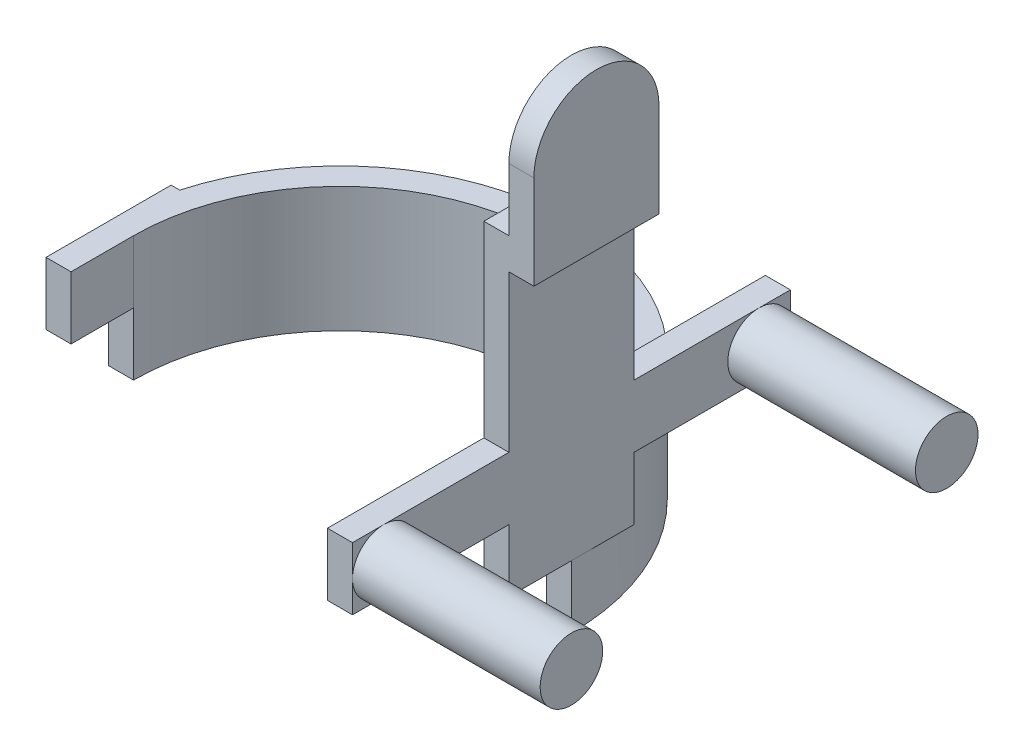
SolidWorks part; units mm, degrees
ref_plane "Front" through (0, 0, 0) normal (0, 0, 1) x (1, 0, 0)
ref_plane "Top" through (0, 0, 0) normal (0, 1, 0) x (1, 0, 0)
ref_plane "Right" through (0, 0, 0) normal (1, 0, 0) x (0, 0, -1)
sketch "草图1" plane through (0, 0, 0) normal (0, 1, 0) x (1, 0, 0)
  line L0 (-72.3418, 0) -> (74, 0) construction
  line L1 (0, 74) -> (0, -74) construction
  line L3 (-74, 20) -> (-71.2461, 20)
  line L4 (-74, 20) -> (-74, -20)
  line L5 (-74, -20) -> (-66, -20)
  line L6 (-66, 0) -> (-66, -20)
  line L7 (74, 20) -> (71.2461, 20)
  line L8 (74, 20) -> (74, -20)
  line L9 (74, -20) -> (66, -20)
  line L10 (66, 0) -> (66, -20)
  arc A0 (71.2461, 20) -> (-71.2461, 20) centre (0, 0) ccw
  arc A1 (66, 0) -> (-66, 0) centre (0, 0) ccw
  dimension "D1" = 40
  dimension "D2" = 20
  dimension "D3" = 8
  dimension "D4" = 8
  dimension "D6" = 40
  dimension "D7" = 20
extrude "凸台-拉伸1" add sketch "草图1" along normal blind 40
sketch "草图2" plane through (0, 40, 0) normal (0, 1, 0) x (1, 0, 0)
  line L1 (-74, -20) -> (-66, -20)
  line L2 (-74, -20) -> (-74, 20)
  line L3 (-74, 20) -> (-66, 20)
  line L4 (-66, -20) -> (-66, 20)
  line L5 (66, -20) -> (74, -20)
  line L6 (66, -20) -> (66, 20)
  line L7 (66, 20) -> (74, 20)
  line L8 (74, -20) -> (74, 20)
  dimension "D1" = 8
extrude "凸台-拉伸2" add sketch "草图2" along normal blind 80
sketch "草图4" plane through (-74, 0, 0) normal (-1, 0, 0) x (0, 0, 1)
  line L1 (-20, 40) -> (29.7839, 40)
  line L2 (-20, 40) -> (-20, 153.9823)
  line L3 (-20, 153.9823) -> (29.7839, 153.9823)
  line L4 (29.7839, 40) -> (29.7839, 153.9823)
extrude "切除-拉伸3" cut sketch "草图4" against normal blind 10
sketch "草图5" plane through (0, 0, 0) normal (0, -1, 0) x (1, 0, 0)
  line L0 (66, 0) -> (66, 20) construction
  line L1 (-71.2461, 20) -> (-66, 20)
  line L3 (-74, 0) -> (-66, 0)
  line L4 (-66, 20) -> (-66, 0)
  line L5 (71.2461, 20) -> (66, 20)
  line L7 (74, 0) -> (66, 0)
  line L8 (66, 20) -> (66, 0)
  arc A0 (-66, 0) -> (66, 0) centre (0, 0) ccw construction
  arc A1 (-74, 0) -> (74, 0) centre (0, 0) ccw
  circle A2 centre (0, 0) radius 84.7622
  arc A3 (71.2461, 20) -> (-71.2461, 20) centre (0, 0) ccw
extrude "切除-拉伸4" cut sketch "草图5" against normal blind 20
sketch "草图6" plane through (74, 0, 0) normal (1, 0, 0) x (0, 0, -1)
  line L0 (66, 40) -> (0, 40) construction
  line L1 (70, 40) -> (-70, 40)
  line L2 (70, 40) -> (70, 60)
  line L3 (70, 60) -> (-70, 60)
  line L4 (-70, 40) -> (-70, 60)
  line L5 (0, 0) -> (0, 148.7503) construction
  dimension "D1" = 140
  dimension "D2" = 70
  dimension "D3" = 20
extrude "凸台-拉伸3" add sketch "草图6" against normal blind 8
sketch "草图7" plane through (74, 0, 0) normal (1, 0, 0) x (0, 0, -1)
  circle A0 centre (-60, 50) radius 10
  circle A1 centre (60, 50) radius 10
extrude "凸台-拉伸4" add sketch "草图7" along normal blind 60
sketch "草图9" plane through (0, 0, -20) normal (0, 0, -1) x (-1, 0, 0)
  line L0 (-74, 120) -> (-74, 60) construction
  line L1 (-74, 110) -> (-82, 110)
  line L2 (-74, 110) -> (-74, 160)
  line L3 (-74, 160) -> (-82, 160)
  line L4 (-82, 110) -> (-82, 160)
  line L5 (-74, 120) -> (-66, 120) construction
  point P8 (-78, 110)
  dimension "D1" = 8
  dimension "D2" = 50
  dimension "D3" = 10
extrude "凸台-拉伸5" add sketch "草图9" against normal blind 40
sketch "草图10" plane through (82, 0, 0) normal (1, 0, 0) x (0, 0, -1)
  line L2 (-20, 140) -> (-20, 173.0766)
  line L3 (-20, 173.0766) -> (20, 173.0766)
  line L4 (20, 140) -> (20, 173.0766)
  arc A0 (20, 140) -> (-20, 140) centre (0, 140) ccw
extrude "切除-拉伸5" cut sketch "草图10" against normal blind 40
